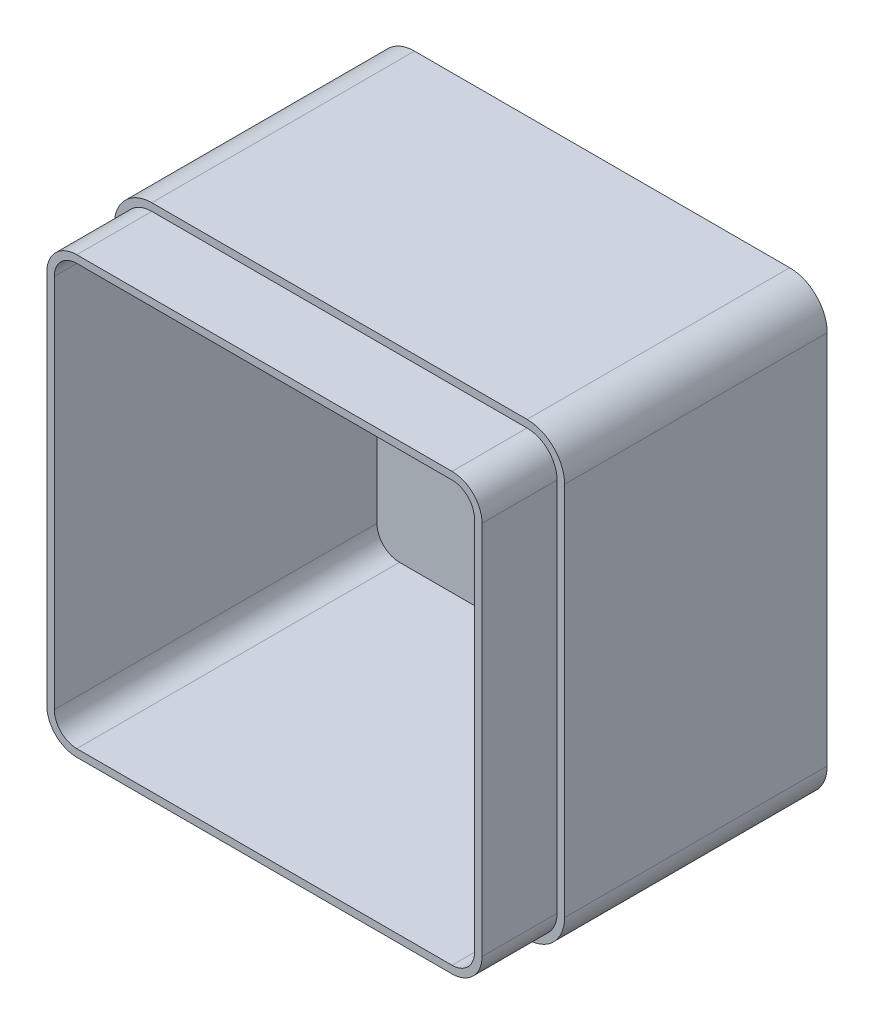
SolidWorks part; units mm, degrees
ref_plane "Front Plane" through (0, 0, 0) normal (0, 0, 1) x (1, 0, 0)
ref_plane "Top Plane" through (0, 0, 0) normal (0, 1, 0) x (1, 0, 0)
ref_plane "Right Plane" through (0, 0, 0) normal (1, 0, 0) x (0, 0, -1)
sketch "Sketch3" plane through (0, 0, 0) normal (0, 0, 1) x (1, 0, 0)
  line L1 (0, 0) -> (120, 0)
  line L2 (0, 0) -> (0, 120)
  line L3 (0, 120) -> (120, 120)
  line L4 (120, 0) -> (120, 120)
  dimension "D1" = 120
  dimension "D2" = 120
extrude "Boss-Extrude1" add sketch "Sketch3" along normal blind 90
fillet "Fillet1" radius 10 4 edges at (120, 0, 45) (0, 0, 45) (0, 120, 45) (120, 120, 45)
shell "Shell1" thickness 4
sketch "Sketch4" plane through (0, 0, 90) normal (0, 0, 1) x (1, 0, 0)
  line L4 (10, 0) -> (110, 0)
  line L5 (120, 10) -> (120, 110)
  line L6 (110, 120) -> (10, 120)
  line L7 (0, 110) -> (0, 10)
  line L8 (10, 0) -> (110, 0)
  line L9 (120, 10) -> (120, 110)
  line L10 (110, 120) -> (10, 120)
  line L11 (0, 110) -> (0, 10)
  line L16 (10, 2) -> (110, 2)
  line L17 (118, 10) -> (118, 110)
  line L18 (110, 118) -> (10, 118)
  line L19 (2, 110) -> (2, 10)
  line L20 (10, 2) -> (110, 2)
  line L21 (118, 10) -> (118, 110)
  line L22 (110, 118) -> (10, 118)
  line L23 (2, 110) -> (2, 10)
  arc A4 (110, 0) -> (120, 10) centre (110, 10) ccw
  arc A5 (120, 110) -> (110, 120) centre (110, 110) ccw
  arc A6 (10, 120) -> (0, 110) centre (10, 110) ccw
  arc A7 (0, 10) -> (10, 0) centre (10, 10) ccw
  arc A8 (110, 0) -> (120, 10) centre (110, 10) ccw
  arc A9 (120, 110) -> (110, 120) centre (110, 110) ccw
  arc A10 (10, 120) -> (0, 110) centre (10, 110) ccw
  arc A11 (0, 10) -> (10, 0) centre (10, 10) ccw
  arc A16 (110, 2) -> (118, 10) centre (110, 10) ccw
  arc A17 (118, 110) -> (110, 118) centre (110, 110) ccw
  arc A18 (10, 118) -> (2, 110) centre (10, 110) ccw
  arc A19 (2, 10) -> (10, 2) centre (10, 10) ccw
  arc A20 (110, 2) -> (118, 10) centre (110, 10) ccw
  arc A21 (118, 110) -> (110, 118) centre (110, 110) ccw
  arc A22 (10, 118) -> (2, 110) centre (10, 110) ccw
  arc A23 (2, 10) -> (10, 2) centre (10, 10) ccw
  dimension "D1" = 0
  dimension "D2" = 2
extrude "Cut-Extrude1" cut sketch "Sketch4" against normal blind 20
